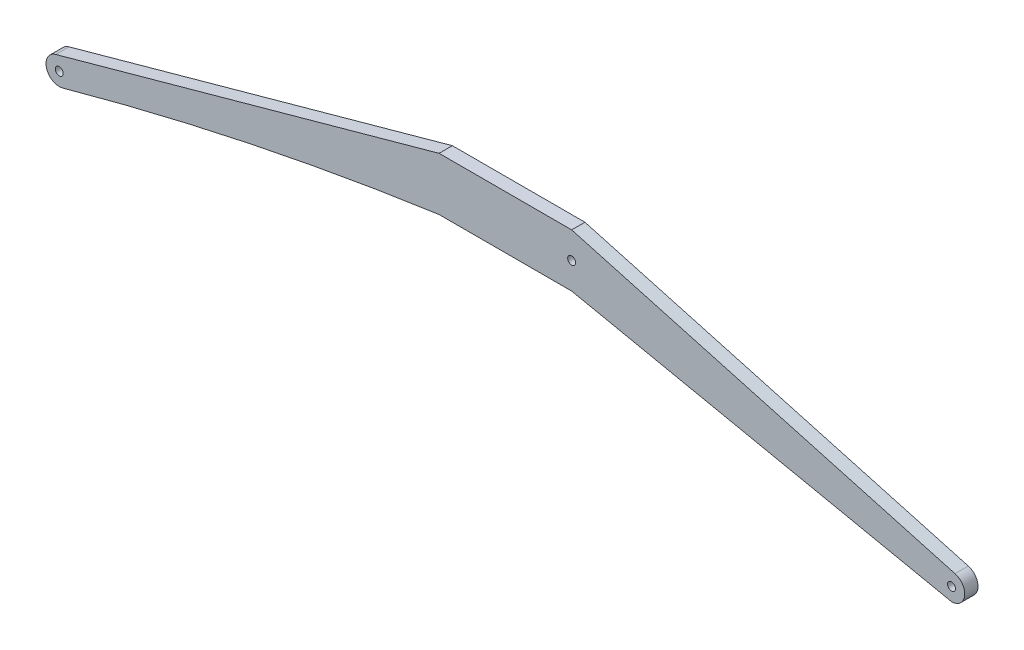
SolidWorks part; units mm, degrees
material "铸造合金钢"
ref_plane "前视基准面" through (0, 0, 0) normal (0, 0, 1) x (1, 0, 0)
ref_plane "上视基准面" through (0, 0, 0) normal (0, 1, 0) x (1, 0, 0)
ref_plane "右视基准面" through (0, 0, 0) normal (1, 0, 0) x (0, 0, -1)
sketch "草图1" plane through (0, 0, 0) normal (0, 0, 1) x (1, 0, 0)
  line L0 (-5, 0) -> (5, 0)
  line L1 (5, 0) -> (33.9137, -8)
  line L2 (0, 7.6205) -> (0, -4.4756)
  line L3 (-5, 0) -> (-33.9137, -8)
  line L4 (-5, -4) -> (5, -4)
  line L5 (-33.9137, -8) -> (-33.3803, -9.9276)
  line L6 (5, -4) -> (33.647, -9.9638)
  arc A0 (-33.9137, -8) -> (-33.3803, -9.9276) centre (-33.647, -8.9638) ccw
  circle A1 centre (-33.647, -8.9638) radius 0.3
  circle A2 centre (33.647, -8.9638) radius 0.3
  arc A3 (33.9137, -8) -> (33.2479, -9.8807) centre (33.647, -8.9638) cw
  arc A4 (-33.3803, -9.9276) -> (-5, -4) centre (27.0336, -228.2761) cw
  circle A5 centre (5, -2) radius 0.3
  point P9 (0, -4)
  dimension "D2" = 2
  dimension "D1" = 8
  dimension "D3" = 90
extrude "凸台-拉伸1" add sketch "草图1" along normal blind 1 contours A3 L1 L0 L2 L4 L6 A5 A2 | L5 A4 L4 L2 L0 L3 A1 | A1 L5 A0
